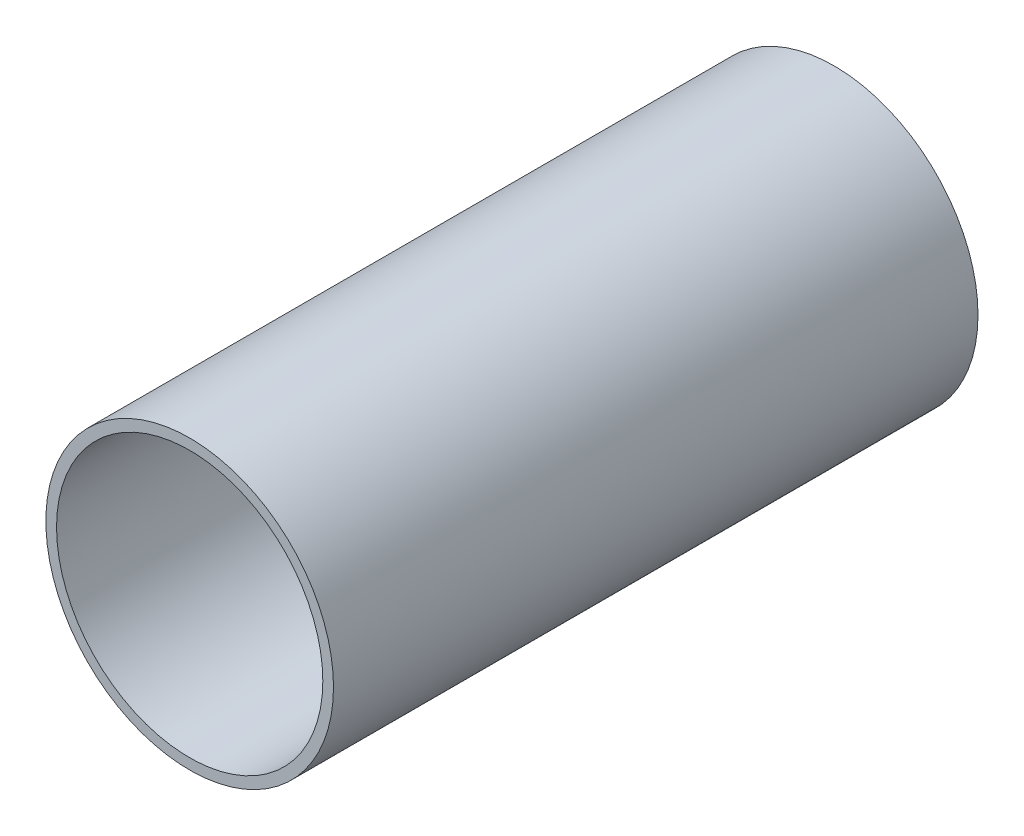
SolidWorks part; units mm, degrees
ref_plane "Front" through (0, 0, 0) normal (0, 0, 1) x (1, 0, 0)
ref_plane "Top" through (0, 0, 0) normal (0, 1, 0) x (1, 0, 0)
ref_plane "Side" through (0, 0, 0) normal (1, 0, 0) x (0, 0, -1)
sketch "PipeSketch" plane through (0, 0, 0) normal (0, 0, 1) x (1, 0, 0)
  circle A0 centre (0, 0) radius 203.2
  circle A1 centre (0, 0) radius 188.1124
  dimension "OuterDiameter" = 406.4
  dimension "InnerDiameter" = 376.2248
extrude "Extrusion" add sketch "PipeSketch" along normal blind 910.6
sketch "FilterSketch" plane through (0, 0, 0) normal (0, 0, 1) x (1, 0, 0)
  circle A0 centre (0, 0) radius 203.2 construction
  dimension "NominalDiameter" = 406.4
